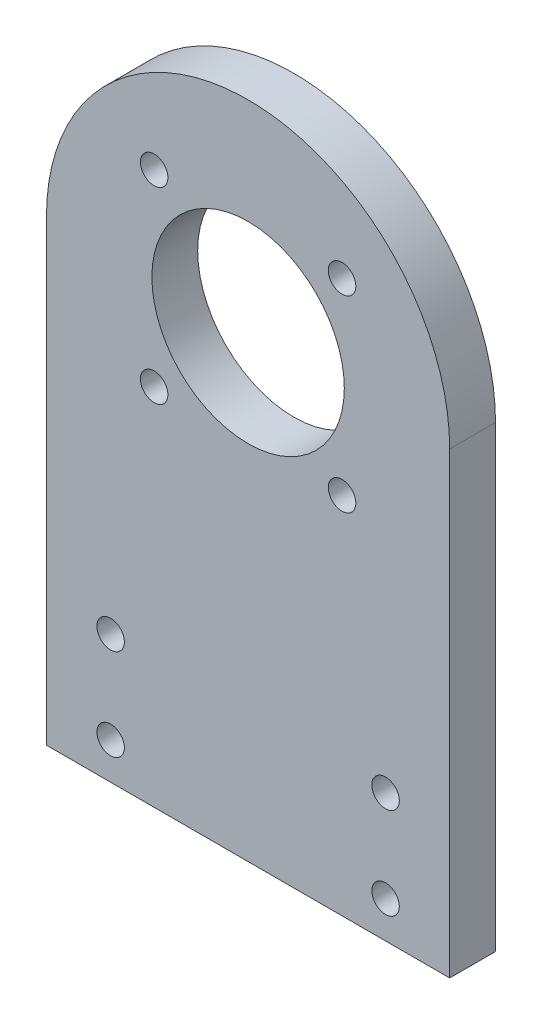
SolidWorks part; units mm, degrees
material "6063-O"
ref_plane "前视基准面" through (0, 0, 0) normal (0, 0, 1) x (1, 0, 0)
ref_plane "上视基准面" through (0, 0, 0) normal (0, 1, 0) x (1, 0, 0)
ref_plane "右视基准面" through (0, 0, 0) normal (1, 0, 0) x (0, 0, -1)
sketch "草图1" plane through (0, 0, 0) normal (0, 0, 1) x (1, 0, 0)
  line L0 (0, 148.1001) -> (0, -47.4393) construction
  line L1 (-22, 0) -> (22, 0)
  line L2 (-22, 0) -> (-22, 50)
  line L3 (-22, 50) -> (22, 50) construction
  line L4 (22, 0) -> (22, 50)
  line L5 (0, 50) -> (12.3744, 62.3744) construction
  arc A0 (22, 50) -> (-22, 50) centre (0, 50) ccw
  circle A1 centre (-15, 14) radius 1.5
  circle A2 centre (-15, 4) radius 1.5
  circle A3 centre (15, 4) radius 1.5
  circle A4 centre (15, 14) radius 1.5
  circle A5 centre (0, 50) radius 10.5
  circle A6 centre (0, 50) radius 17.5 construction
  circle A7 centre (12.3744, 62.3744) radius 2 construction
  circle A8 centre (12.3744, 37.6256) radius 2 construction
  circle A9 centre (-12.3744, 37.6256) radius 2 construction
  circle A10 centre (-12.3744, 62.3744) radius 2 construction
  point P5 (0, 0)
  point P30 (0, 50)
  dimension "D3" = 3
  dimension "D4" = 3
  dimension "D6" = 10
  dimension "D7" = 7
  dimension "D8" = 21
  dimension "D9" = 35
  dimension "D10" = 45
  dimension "D11" = 4
  dimension "D1" = 44
  dimension "D2" = 50
  dimension "D5" = 4
  dimension "D12" = 4
extrude "凸台-拉伸1" add sketch "草图1" along normal blind 5
sketch "草图2" plane through (0, 0, 0) normal (0, 0, -1) x (-1, 0, 0)
  line L0 (0, 50) -> (32.4134, 50) construction
  line L1 (0, 50) -> (29.0311, 79.0311) construction
  circle A1 centre (0, 50) radius 11.5 construction
  circle A2 centre (0, 50) radius 14.5 construction
  circle A3 centre (10.253, 60.253) radius 1.5
  circle A4 centre (10.253, 39.747) radius 1.5
  circle A5 centre (-10.253, 39.747) radius 1.5
  circle A6 centre (-10.253, 60.253) radius 1.5
  circle A7 centre (0, 50) radius 10.5 construction
  point P18 (0, 50)
  dimension "D2" = 3
  dimension "D5" = 23
  dimension "D3" = 45
  dimension "D1" = 3
  dimension "D4" = 4
extrude "切除-拉伸1" cut sketch "草图2" against normal through all
